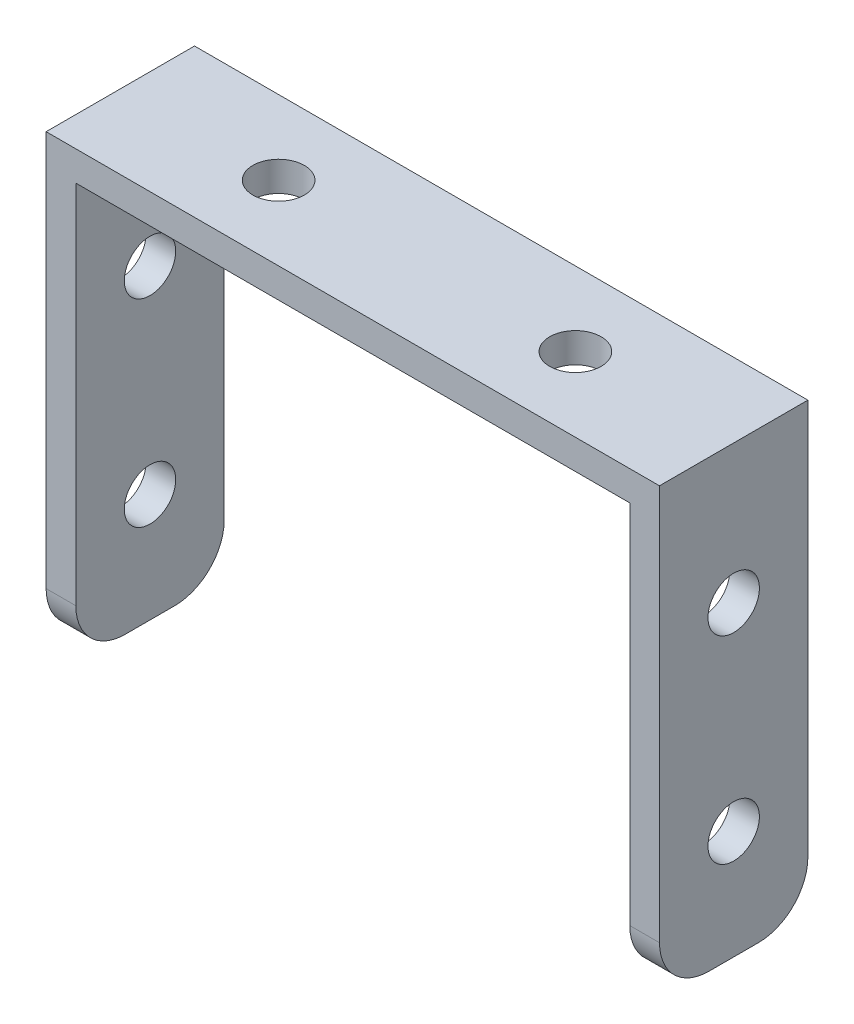
SolidWorks part; units mm, degrees
ref_plane "Plano frontal" through (0, 0, 0) normal (0, 0, 1) x (1, 0, 0)
ref_plane "Plano superior" through (0, 0, 0) normal (0, 1, 0) x (1, 0, 0)
ref_plane "Plano direito" through (0, 0, 0) normal (1, 0, 0) x (0, 0, -1)
sketch "Esboço1" plane through (0, 0, 0) normal (0, 0, 1) x (1, 0, 0)
  line L0 (-31, 0) -> (-28, 0)
  line L1 (-28, 0) -> (-28, 42)
  line L2 (-28, 42) -> (28, 42)
  line L3 (-31, 0) -> (-31, 45)
  line L4 (-31, 45) -> (31, 45)
  line L5 (0, 0) -> (0, 42) construction
  line L6 (31, 0) -> (28, 0)
  line L7 (31, 0) -> (31, 45)
  line L8 (28, 0) -> (28, 42)
  dimension "D1" = 3
  dimension "D2" = 3
  dimension "D3" = 45
  dimension "D4" = 62
extrude "Ressalto-extrusão1" add sketch "Esboço1" along normal blind 15
sketch "Esboço2" plane through (0, 45, 0) normal (0, 1, 0) x (1, 0, 0)
  line L0 (15, -7.5) -> (-15, -7.5) construction
  line L1 (31, -15) -> (31, 0) construction
  circle A0 centre (-15, -7.5) radius 2.6
  circle A1 centre (15, -7.5) radius 2.6
  point P4 (0, -7.5)
  point P7 (31, -7.5)
  dimension "D1" = 5.2
  dimension "D2" = 30
extrude "Corte-extrusão1" cut sketch "Esboço2" against normal blind 15
sketch "Esboço3" plane through (31, 0, 0) normal (1, 0, 0) x (0, 0, -1)
  line L0 (-7.5, 31) -> (-7.5, 11) construction
  line L1 (-15, 0) -> (0, 0) construction
  line L3 (-15, 0) -> (-15, 45) construction
  line L4 (-15, 42) -> (-15, 0) construction
  line L5 (-15, 42) -> (-15, 0)
  circle A0 centre (-7.5, 11) radius 2.6
  circle A1 centre (-7.5, 31) radius 2.6
  point P4 (-7.5, 21)
  point P5 (-7.5, 0)
  point P9 (-15, 21)
  dimension "D2" = 5.2
  dimension "D1" = 20
extrude "Corte-extrusão2" cut sketch "Esboço3" against normal through all
fillet "Filete1" radius 5 4 edges at (-29.5, 0, 15) (-29.5, 0, 0) (29.5, 0, 0) (29.5, 0, 15)
